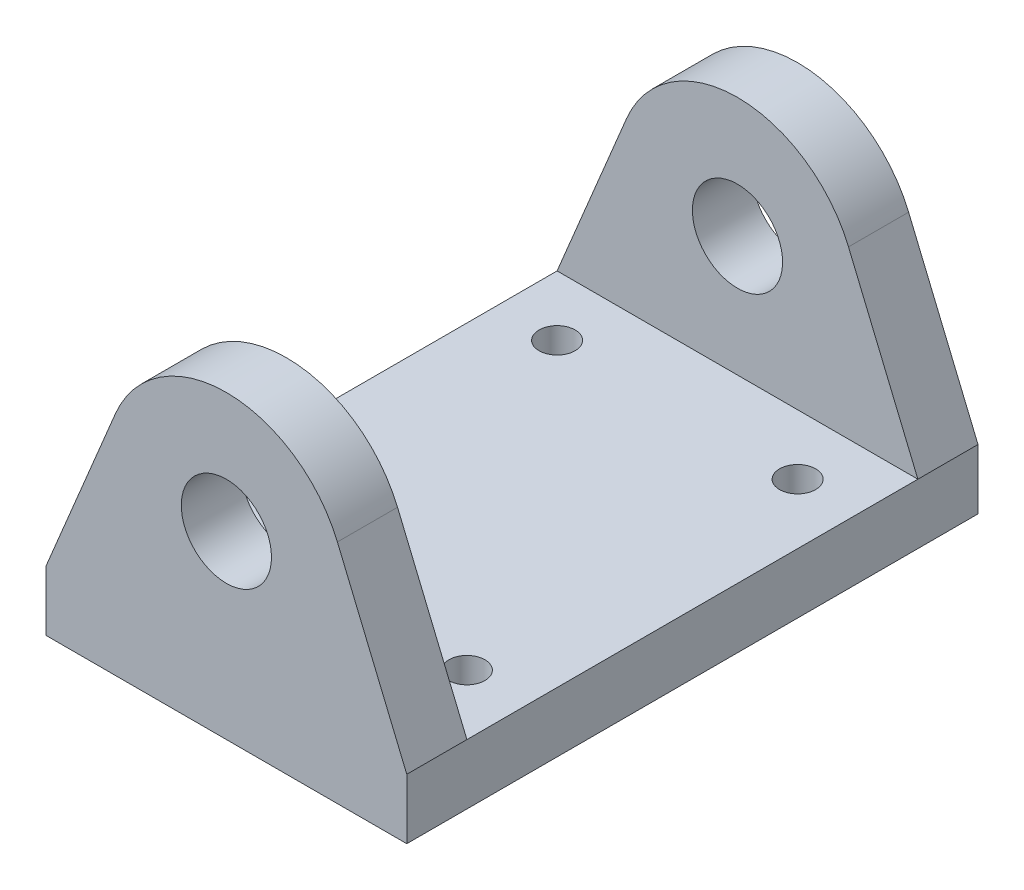
SolidWorks part; units mm, degrees
ref_plane "Front Plane" through (0, 0, 0) normal (0, 0, 1) x (1, 0, 0)
ref_plane "Top Plane" through (0, 0, 0) normal (0, 1, 0) x (1, 0, 0)
ref_plane "Right Plane" through (0, 0, 0) normal (1, 0, 0) x (0, 0, -1)
sketch "Sketch1" plane through (0, 0, 0) normal (0, 0, 1) x (1, 0, 0)
  line L0 (-15, -10) -> (15, -10)
  line L1 (-15, -10) -> (-9.2308, 3.8462)
  line L2 (15, -10) -> (9.2308, 3.8462)
  circle A0 centre (0, 0) radius 3.75
  arc A1 (9.2308, 3.8462) -> (-9.2308, 3.8462) centre (0, 0) ccw
  point P6 (0, -10)
  dimension "D1" = 7.5
  dimension "D2" = 20
  dimension "D3" = 30
  dimension "D4" = 10
extrude "Boss-Extrude1" add sketch "Sketch1" along normal mid plane 47.5
sketch "Sketch2" plane through (0, -10, 0) normal (0, -1, 0) x (1, 0, 0)
  line L4 (-15, -23.75) -> (15, -23.75)
  line L5 (15, -23.75) -> (15, 23.75)
  line L6 (15, 23.75) -> (-15, 23.75)
  line L7 (-15, 23.75) -> (-15, -23.75)
  line L8 (-15, -23.75) -> (15, -23.75)
  line L9 (15, -23.75) -> (15, 23.75)
  line L10 (15, 23.75) -> (-15, 23.75)
  line L11 (-15, 23.75) -> (-15, -23.75)
  dimension "D1" = 0
extrude "Boss-Extrude2" add sketch "Sketch2" along normal blind 5
sketch "Sketch3" plane through (15, 0, 0) normal (1, 0, 0) x (0, 0, -1)
  line L0 (-23.75, -10) -> (23.75, -10) construction
  line L1 (-18.75, -10) -> (18.75, -10)
  line L2 (-18.75, -10) -> (-18.75, 11.5756)
  line L3 (-18.75, 11.5756) -> (18.75, 11.5756)
  line L4 (18.75, -10) -> (18.75, 11.5756)
  line L5 (-23.75, -10) -> (-23.75, 3.8462) construction
  line L6 (23.75, 3.8462) -> (23.75, 10) construction
  point P6 (-18.75, 0.7878)
  dimension "D1" = 5
  dimension "D2" = 5
extrude "Cut-Extrude1" cut sketch "Sketch3" against normal up to vertex (30 mm away)
sketch "Sketch4" plane through (0, -10, 0) normal (0, 1, 0) x (1, 0, 0)
  line L0 (-15, -18.75) -> (-15, 18.75) construction
  line L1 (-15, 18.75) -> (15, 18.75) construction
  line L2 (15, -18.75) -> (15, 18.75) construction
  line L3 (9.2308, -18.75) -> (-9.2308, -18.75) construction
  line L4 (0, 18.75) -> (0, -18.75) construction
  circle A0 centre (-10, 13.75) radius 1.5
  circle A1 centre (10, -13.75) radius 1.5
  circle A2 centre (-10, -13.75) radius 1.5
  circle A3 centre (10, 13.75) radius 1.5
  dimension "D1" = 3
  dimension "D2" = 3
  dimension "D3" = 5
  dimension "D4" = 5
  dimension "D5" = 5
  dimension "D6" = 5
extrude "Cut-Extrude2" cut sketch "Sketch4" against normal up to vertex (5 mm away)
